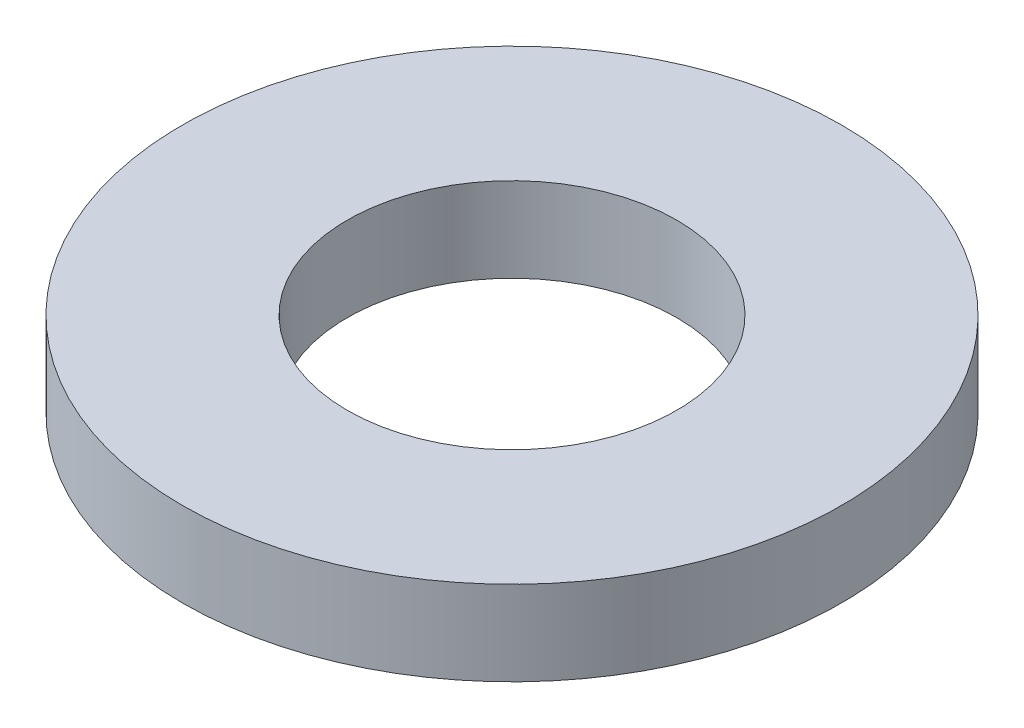
SolidWorks part; units mm, degrees
material "AISI 316 Annealed Stainless Steel Bar (SS)"
ref_plane "Front Plane" through (0, 0, 0) normal (0, 0, 1) x (1, 0, 0)
ref_plane "Top Plane" through (0, 0, 0) normal (0, 1, 0) x (1, 0, 0)
ref_plane "Right Plane" through (0, 0, 0) normal (1, 0, 0) x (0, 0, -1)
sketch "Sketch1" plane through (0, 0, 0) normal (0, 1, 0) x (1, 0, 0)
  circle A0 centre (0, 0) radius 3.9624
  dimension "OD" = 7.9248
extrude "Boss-Extrude1" add sketch "Sketch1" along normal blind 1.016
sketch "Sketch5" plane through (0, 1.016, 0) normal (0, 1, 0) x (-1, 0, 0)
  circle A0 centre (0, 0) radius 1.9812
  dimension "ID" = 3.9624
extrude "Cut-Extrude1" cut sketch "Sketch5" against normal through all
